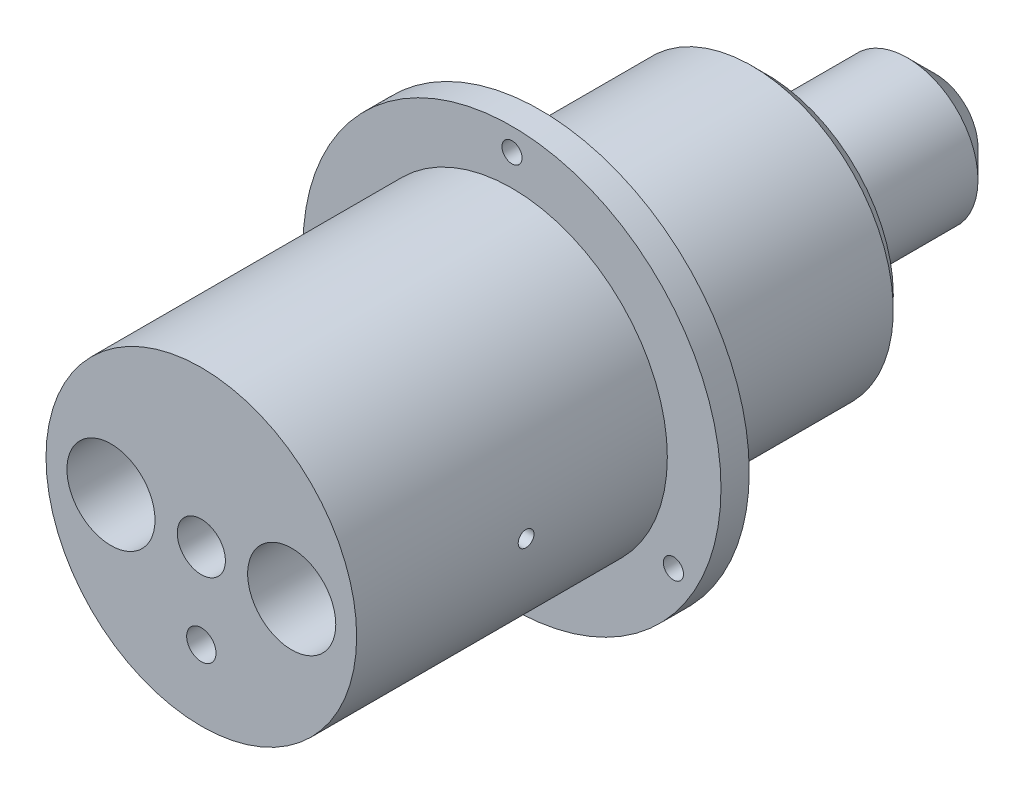
SolidWorks part; units mm, degrees
other "DetailItem1"
ref_plane "Front Plane" through (0, 0, 0) normal (0, 0, 1) x (1, 0, 0)
ref_plane "Top Plane" through (0, 0, 0) normal (0, 1, 0) x (1, 0, 0)
ref_plane "Right Plane" through (0, 0, 0) normal (1, 0, 0) x (0, 0, -1)
sketch "Sketch1" plane through (0, 0, 0) normal (0, 0, 1) x (1, 0, 0)
  circle A0 centre (0, 0) radius 25.4
  dimension "D1" = 50.8
extrude "Boss-Extrude1" add sketch "Sketch1" along normal blind 38.1 and the other way blind 44.45
sketch "Sketch2" plane through (0, 0, 38.1) normal (0, 0, 1) x (1, 0, 0)
  circle A0 centre (0, 0) radius 17.4625
  dimension "D1" = 34.925
extrude "Cut-Extrude3" cut sketch "Sketch2" against normal blind 63.5 flip side to cut
fillet "Fillet1" [suppressed] radius 2.54
sketch "Sketch3" plane through (0, 0, 0) normal (0, 0, 1) x (1, 0, 0)
  circle A0 centre (0, 0) radius 23.495
  dimension "D1" = 46.99
extrude "Boss-Extrude2" add sketch "Sketch3" along normal blind 3.175
fillet "Fillet2" [suppressed] radius 6.35
hole_wizard "1/4-28 Tapped Hole1" positions "Sketch5" profile "Sketch4" tap size "1/4-28" standard "ANSI Inch"
sketch "Sketch5" plane through (0, 0, 38.1) normal (0, 0, 1) x (1, 0, 0)
  point P0 (0, 0)
sketch "Sketch4" plane through (0, 0, 38.1) normal (1, 0, 0) x (0, -1, 0)
  line L0 (0, 0) -> (0, 14.5057)
  line L1 (0, 14.5057) -> (2.7051, 12.8803)
  line L2 (2.7051, 12.8803) -> (2.7051, 0)
  line L5 (2.7051, 0) -> (0, 0)
  line L10 (0, 14.5057) -> (-2.7051, 12.8803) construction
  line L11 (0, -6.35) -> (0, 107.95) construction
  dimension "Tap Drill Dia." = 5.4102
  dimension "Tap Drill Depth" = 12.8803
  dimension "Drill Angle" = 118
cosmetic thread "Hole Thread1" parameters "D1"=12.8803, "D2"=6.35
hole_wizard "#2 Clearance Hole1" positions "Sketch8" profile "Sketch6" hole size "#2" standard "ANSI Inch"
sketch "Sketch8" plane through (0, 0, 3.175) normal (0, 0, 1) x (1, 0, 0)
  point P2 (0, 20.955)
  dimension "D2" = 20.955
sketch "Sketch6" plane through (0, 20.955, 3.175) normal (1, 0, 0) x (0, -1, 0)
  line L0 (0, 0) -> (0, 13.5595)
  line L1 (0, 13.5595) -> (1.1303, 12.8803)
  line L2 (1.1303, 12.8803) -> (1.1303, 0)
  line L5 (1.1303, 0) -> (0, 0)
  line L10 (0, 13.5595) -> (-1.1303, 12.8803) construction
  line L11 (0, -6.35) -> (0, 107.95) construction
  dimension "Hole Dia." = 2.2606
  dimension "Hole Depth" = 12.8803
  dimension "Drill Angle" = 118
sketch "Sketch9" plane through (0, 0, -44.45) normal (0, 0, -1) x (-1, 0, 0)
  circle A0 centre (0, 0) radius 0.8636
  dimension "D1" = 1.7272
extrude "Cut-Extrude4" cut sketch "Sketch9" against normal through all
sketch "Sketch12" plane through (0, 0, 38.1) normal (0, 0, 1) x (1, 0, 0)
  circle A0 centre (-10.16, 0) radius 4.953
  circle A1 centre (10.16, 0) radius 4.953
  dimension "D7" = 9.906
  dimension "D8" = 9.906
  dimension "D1" = 20.32
  dimension "D2" = 10.16
extrude "Cut-Extrude5" cut sketch "Sketch12" against normal blind 45.72
sketch "Sketch17" plane through (0, 0, 38.1) normal (0, 0, 1) x (1, 0, 0)
  circle A0 centre (0, -9.525) radius 1.651
  dimension "D2" = 3.302
  dimension "D1" = 9.525
  dimension "D3" = 0
extrude "Cut-Extrude7" cut sketch "Sketch17" against normal blind 44.45
sketch "Sketch22" plane through (0, 0, -44.45) normal (0, 0, -1) x (-1, 0, 0)
  circle A0 centre (0, 0) radius 7.9375
extrude "Cut-Extrude9" cut sketch "Sketch22" against normal blind 19.05 flip side to cut
chamfer "Chamfer1" distance 3.175 angle 45 2 edges at (-17.4625, 0, -25.4) (-7.9375, 0, -44.45)
hole_wizard "#2-56 Tapped Hole3" positions "3DSketch1" profile "Sketch23" tap size "#2-56" standard "ANSI Inch"
sketch3d "3DSketch1"
  point P0 (0, -17.4625, 19.05)
sketch "Sketch23" plane through (0, -17.4625, 19.05) normal (1, 0, 0) x (0, 0, -1)
  line L0 (0, 0) -> (0, 6.2865)
  line L1 (0, 6.2865) -> (0.889, 6.2865)
  line L2 (0.889, 6.2865) -> (0.889, 0)
  line L5 (0.889, 0) -> (0, 0)
  line L11 (0, -6.35) -> (0, 107.95) construction
  dimension "Thru Tap Drill Dia." = 1.778
  dimension "Thru Tap Drill Depth" = 6.2865
cosmetic thread "Hole Thread3" parameters "D2"=2.1844
hole_wizard "#2-56 Tapped Hole4" positions "3DSketch2" profile "Sketch24" tap size "#2-56" standard "ANSI Inch"
sketch3d "3DSketch2"
  point P0 (17.4625, 0, 19.05)
sketch "Sketch24" plane through (17.4625, 0, 19.05) normal (0, 1, 0) x (0, 0, -1)
  line L0 (0, 0) -> (0, 2.3495)
  line L1 (0, 2.3495) -> (0.889, 2.3495)
  line L2 (0.889, 2.3495) -> (0.889, 0)
  line L5 (0.889, 0) -> (0, 0)
  line L11 (0, -6.35) -> (0, 107.95) construction
  dimension "Thru Tap Drill Dia." = 1.778
  dimension "Thru Tap Drill Depth" = 2.3495
cosmetic thread "Hole Thread4" parameters "D2"=2.1844
mirror "Mirror2" about plane through (0, 0, 0) normal (1, 0, 0) of "#2-56 Tapped Hole4"
pattern_circular "CirPattern1" count 3 over 360 about axis through (0, 0, 0) along (0, 0, 1) of "#2 Clearance Hole1"
sketch "Sketch25" plane through (0, 0, -25.4) normal (0, 0, -1) x (-1, 0, 0)
  circle A0 centre (0, 0) radius 15.875
  dimension "D1" = 31.75
extrude "Cut-Extrude10" cut sketch "Sketch25" against normal up to surface (25.4 mm away) flip side to cut up to face at (19.2779, -10.4775, 0)
equation "\"D2@Sketch12\"=\"D1@Sketch12\"/2"
equation "\"D8@Sketch12\"=\"D7@Sketch12\""
